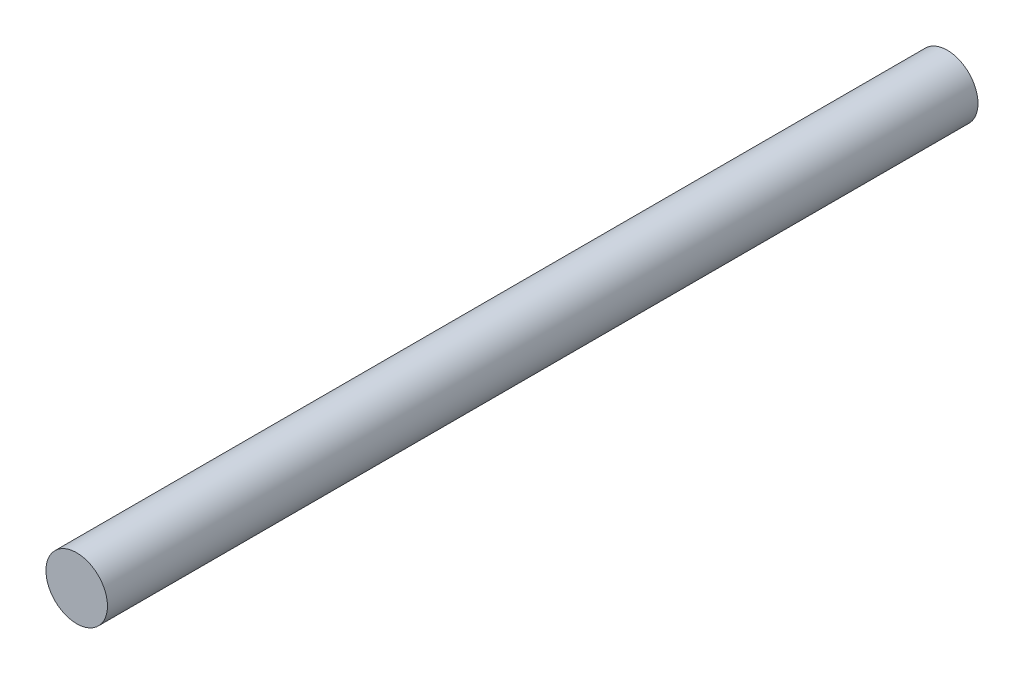
SolidWorks part; units mm, degrees
ref_plane "Front Plane" through (0, 0, 0) normal (0, 0, 1) x (1, 0, 0)
ref_plane "Top Plane" through (0, 0, 0) normal (0, 1, 0) x (1, 0, 0)
ref_plane "Right Plane" through (0, 0, 0) normal (1, 0, 0) x (0, 0, -1)
sketch "Sketch2" plane through (0, 0, 0) normal (0, 0, 1) x (1, 0, 0)
  circle A0 centre (0, 0) radius 15.9
extrude "Boss-Extrude1" add sketch "Sketch2" along normal blind 450
